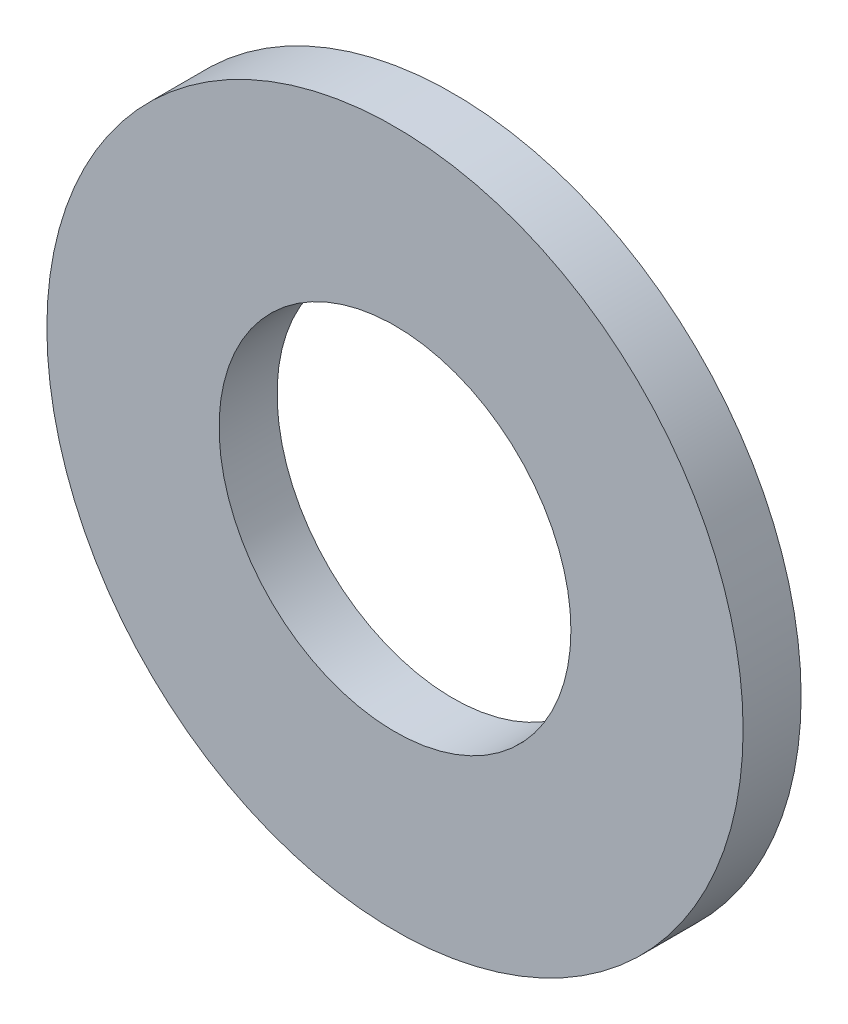
SolidWorks part; units mm, degrees
material "Rulon LR"
ref_plane "Front Plane" through (0, 0, 0) normal (0, 0, 1) x (1, 0, 0)
ref_plane "Top Plane" through (0, 0, 0) normal (0, 1, 0) x (1, 0, 0)
ref_plane "Right Plane" through (0, 0, 0) normal (1, 0, 0) x (0, 0, -1)
sketch "Sketch1" plane through (0, 0, 0) normal (0, 0, 1) x (1, 0, 0)
  circle A0 centre (0, 0) radius 9.525
  circle A1 centre (0, 0) radius 4.8133
  dimension "D1" = 19.05
  dimension "ID" = 9.6266
extrude "Extrude1" add sketch "Sketch1" along normal mid plane 1.5875
sketch "Sketch2" plane through (0, 0, 0) normal (1, 0, 0) x (0, 0, -1)
  line L0 (-0.7937, -4.8133) -> (0.7937, -4.8133) construction
  line L3 (0.7937, 4.8133) -> (-0.7937, 4.8133) construction
  line L5 (-0.7937, -4.8133) -> (0.7937, -4.8133)
  line L6 (0.7937, 4.8133) -> (-0.7937, 4.8133)
sketch "Sketch4" plane through (0, 0, 0.7937) normal (0, 0, 1) x (1, 0, 0)
  line L0 (0, 0) -> (-3.4035, 3.4035)
  line L1 (0, -0.8731) -> (0, 0.8731) construction
  circle A0 centre (0, 0) radius 4.8133 construction
  dimension "D1" = 45
